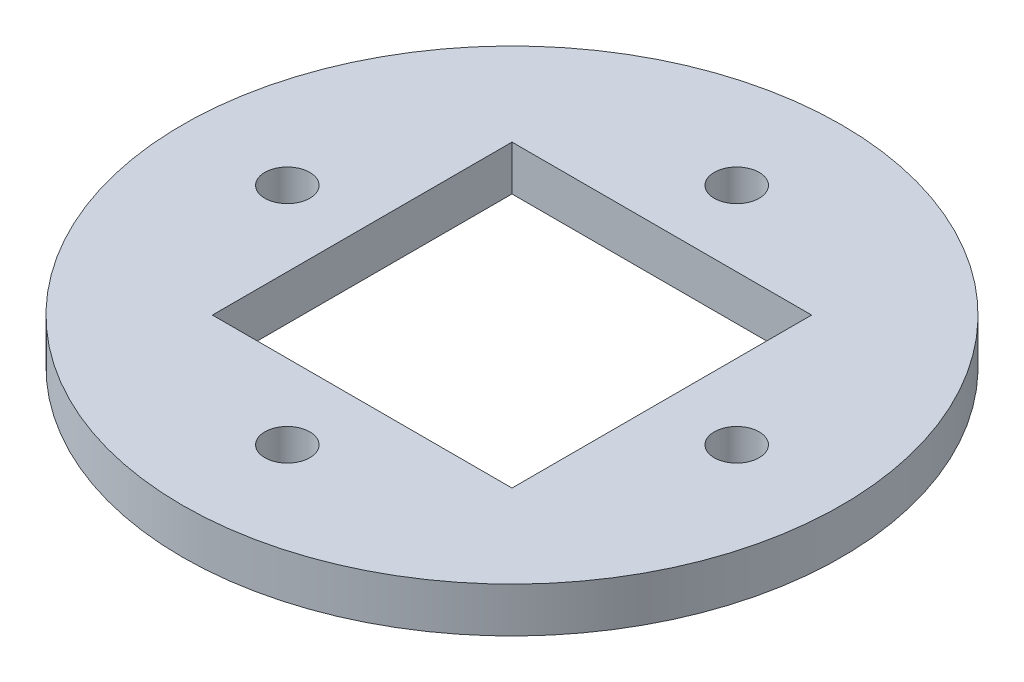
SolidWorks part; units mm, degrees
ref_plane "Front Plane" through (0, 0, 0) normal (0, 0, 1) x (1, 0, 0)
ref_plane "Top Plane" through (0, 0, 0) normal (0, 1, 0) x (1, 0, 0)
ref_plane "Right Plane" through (0, 0, 0) normal (1, 0, 0) x (0, 0, -1)
sketch "Sketch1" plane through (0, 0, 0) normal (0, 1, 0) x (1, 0, 0)
  line L1 (-10, -10) -> (10, -10)
  line L2 (-10, -10) -> (-10, 10)
  line L3 (-10, 10) -> (10, 10)
  line L4 (10, -10) -> (10, 10)
  line L5 (-10, -10) -> (10, 10) construction
  line L6 (-10, 10) -> (10, -10) construction
  circle A0 centre (0, 0) radius 22
  circle A1 centre (-15, 0) radius 1.5
  circle A2 centre (0, 15) radius 1.5
  circle A3 centre (15, 0) radius 1.5
  circle A4 centre (0, -15) radius 1.5
  point P14 (0, 0)
  dimension "D1" = 44
  dimension "D3" = 3
  dimension "D2" = 15
  dimension "D5" = 20
  dimension "D4" = 4
extrude "Boss-Extrude1" add sketch "Sketch1" along normal blind 3
